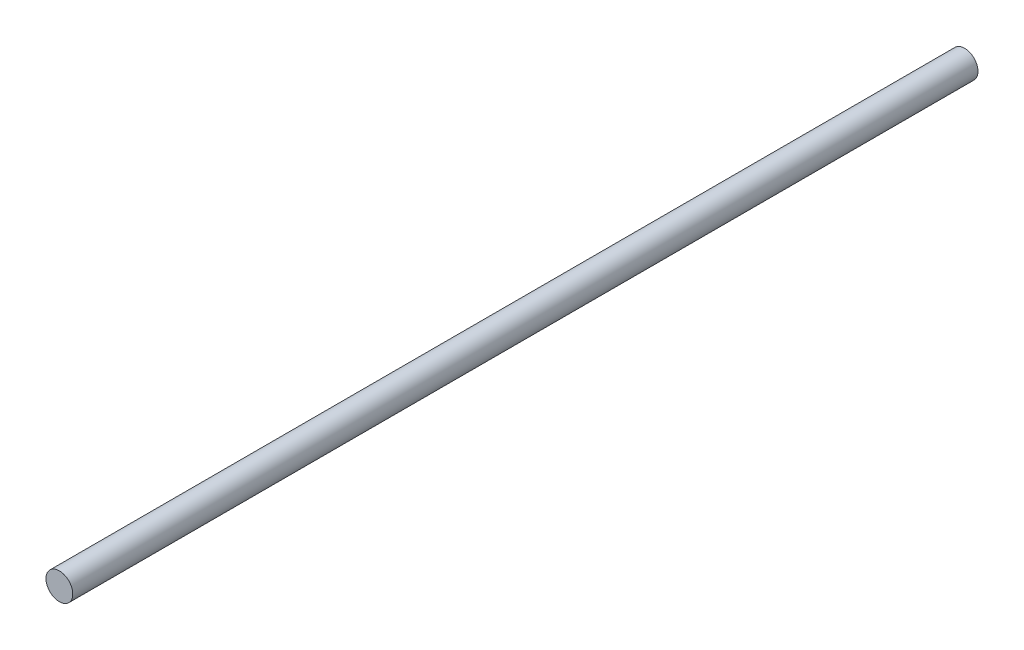
SolidWorks part; units mm, degrees
ref_plane "Front Plane" through (0, 0, 0) normal (0, 0, 1) x (1, 0, 0)
ref_plane "Top Plane" through (0, 0, 0) normal (0, 1, 0) x (1, 0, 0)
ref_plane "Right Plane" through (0, 0, 0) normal (1, 0, 0) x (0, 0, -1)
sketch "Sketch1" plane through (0, 0, 0) normal (0, 0, 1) x (1, 0, 0)
  circle A0 centre (0, 0) radius 10
  dimension "D1" = 20
extrude "Boss-Extrude1" add sketch "Sketch1" along normal mid plane 676
